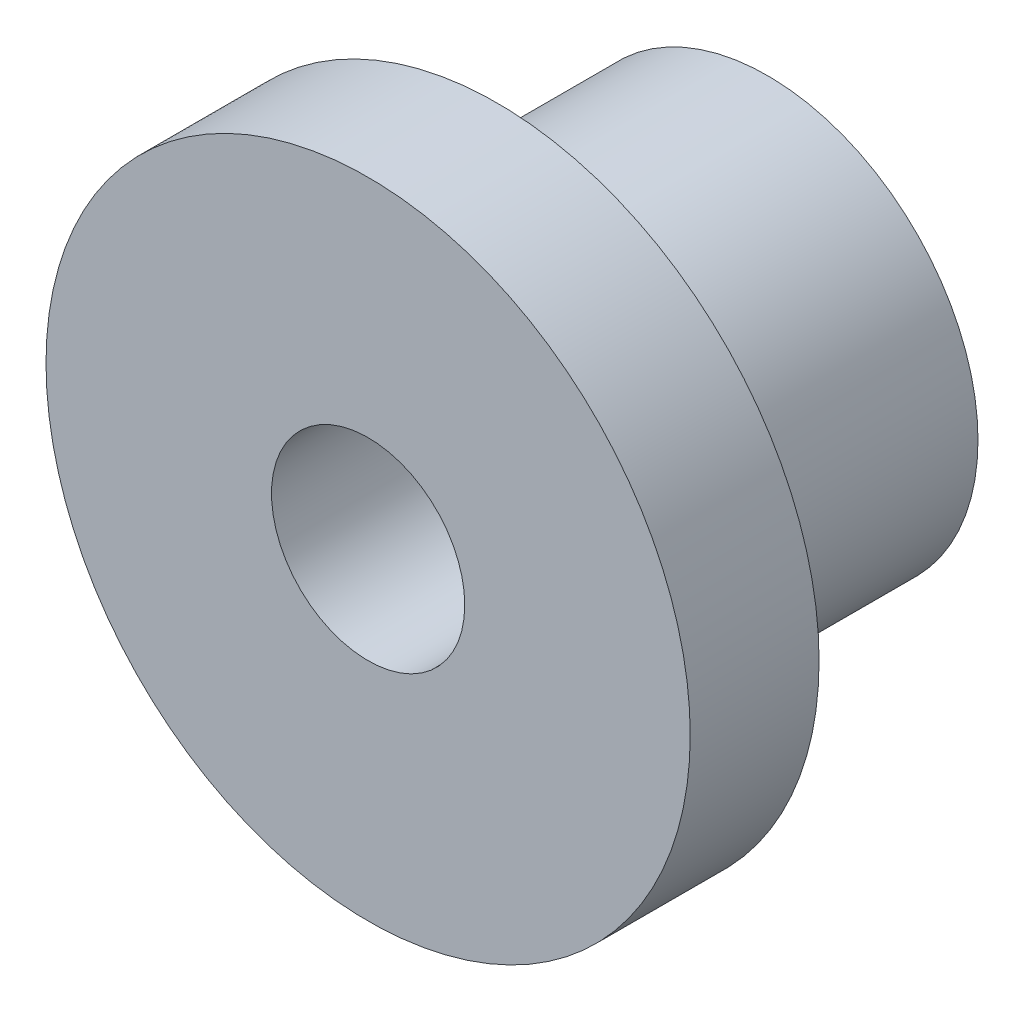
SolidWorks part; units mm, degrees
ref_plane "Front Plane" through (0, 0, 0) normal (0, 0, 1) x (1, 0, 0)
ref_plane "Top Plane" through (0, 0, 0) normal (0, 1, 0) x (1, 0, 0)
ref_plane "Right Plane" through (0, 0, 0) normal (1, 0, 0) x (0, 0, -1)
sketch "Sketch1" plane through (0, 0, 0) normal (0, 0, 1) x (1, 0, 0)
  circle A0 centre (0, 0) radius 4.9
  circle A1 centre (0, 0) radius 2.25
  dimension "D1" = 9.8
  dimension "D2" = 4.5
extrude "Boss-Extrude1" add sketch "Sketch1" along normal mid plane 6.3
sketch "Sketch2" plane through (0, 0, 3.15) normal (0, 0, 1) x (1, 0, 0)
  circle A0 centre (0, 0) radius 2.25
  circle A1 centre (0, 0) radius 7.5
  dimension "D1" = 15
  dimension "D2" = 4.5
extrude "Boss-Extrude2" add sketch "Sketch2" along normal blind 3
